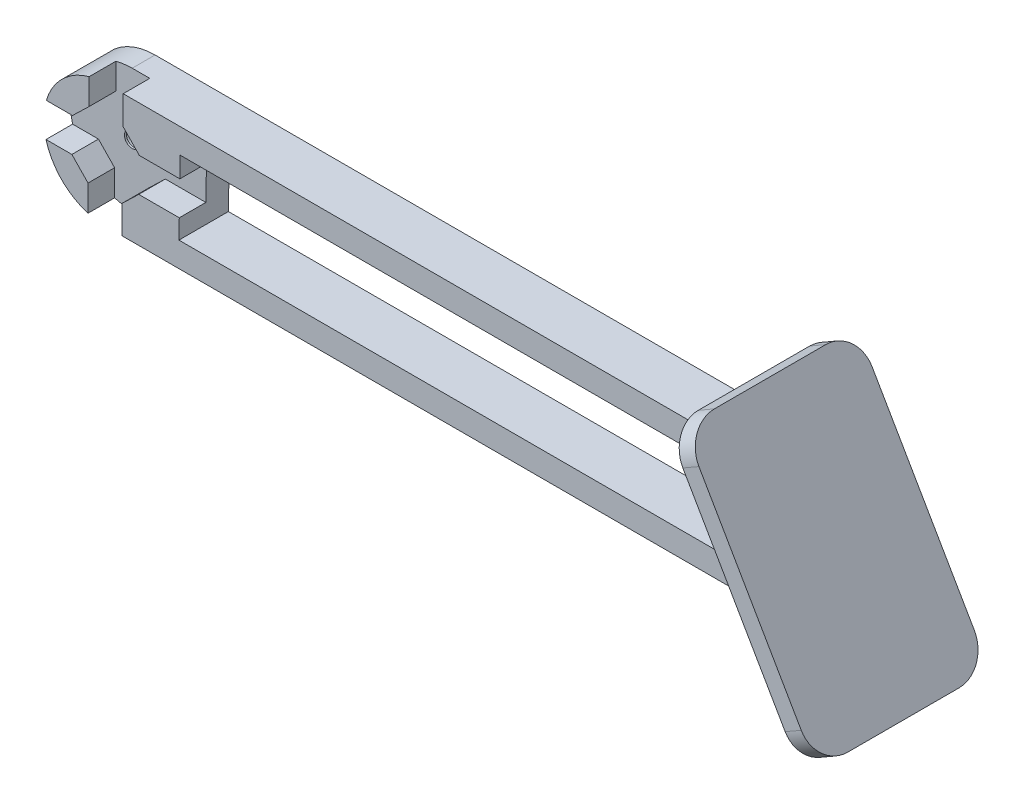
SolidWorks part; units mm, degrees
ref_plane "Plan de face" through (0, 0, 0) normal (0, 0, 1) x (1, 0, 0)
ref_plane "Plan de dessus" through (0, 0, 0) normal (0, 1, 0) x (1, 0, 0)
ref_plane "Plan de droite" through (0, 0, 0) normal (1, 0, 0) x (0, 0, -1)
sketch "Esquisse1" plane through (0, 0, 0) normal (0, 0, 1) x (1, 0, 0)
  line L0 (60, -10.9971) -> (60, 26.1419) construction
  line L1 (0, 0) -> (120, 0)
  line L3 (0, 20) -> (120, 20)
  arc A0 (0, 0) -> (0, 20) centre (0, 10) cw
  arc A1 (120, 0) -> (120, 20) centre (120, 10) ccw
  point P9 (60, 0)
  point P11 (60, 20)
  dimension "D3" = 10
  dimension "D1" = 20
  dimension "D2" = 60
extrude "Boss.-Extru.1" add sketch "Esquisse1" along normal blind 8
sketch "Esquisse13" plane through (0, 0, 8) normal (0, 0, 1) x (1, 0, 0)
  circle A0 centre (0, 10) radius 4
  arc A1 (0, 20) -> (0, 0) centre (0, 10) ccw construction
  dimension "D1" = 8
extrude "Enlèv. mat.-Extru.9" cut sketch "Esquisse13" against normal blind 4.3
sketch "Esquisse14" plane through (0, 0, 8) normal (0, 0, 1) x (1, 0, 0)
  line L0 (2.6554, 4.5441) -> (2.6554, -2.0086)
  line L1 (-2.6554, 22.0086) -> (2.8446, 21.9124)
  line L2 (-2.8446, -1.9124) -> (-2.8446, 4.6403)
  line L4 (12.0086, 12.6554) -> (11.9124, 7.1554)
  line L7 (2.6554, -2.0086) -> (-2.8446, -1.9124)
  line L10 (-12.0086, 7.3446) -> (-11.9124, 12.8446)
  line L12 (5.4559, 12.6554) -> (2.8446, 15.3597)
  line L13 (2.6554, 4.5441) -> (5.3597, 7.1554)
  line L14 (-2.6554, 15.4559) -> (-5.3597, 12.8446)
  line L15 (-5.4559, 7.3446) -> (-2.8446, 4.6403)
  line L16 (5.3597, 7.1554) -> (11.9124, 7.1554)
  line L17 (5.4559, 12.6554) -> (12.0086, 12.6554)
  line L18 (2.8446, 15.3597) -> (2.8446, 21.9124)
  line L19 (-2.6554, 15.4559) -> (-2.6554, 22.0086)
  line L20 (-5.3597, 12.8446) -> (-11.9124, 12.8446)
  line L21 (-5.4559, 7.3446) -> (-12.0086, 7.3446)
  circle A3 centre (0, 10) radius 6.0678 construction
  dimension "D1" = 5.5
  dimension "D2" = 6.5527
extrude "Enlèv. mat.-Extru.10" cut sketch "Esquisse14" against normal blind 4.3
sketch "Esquisse15" plane through (0, 0, 0) normal (0, 0, -1) x (-1, 0, 0)
  circle A0 centre (0, 10) radius 2.5
  arc A1 (0, 0) -> (0, 20) centre (0, 10) ccw construction
  dimension "D1" = 5
extrude "Enlèv. mat.-Extru.11" cut sketch "Esquisse15" against normal blind 3.4
sketch "Esquisse16" plane through (0, 0, 3.4) normal (0, 0, -1) x (-1, 0, 0)
  circle A0 centre (0, 10) radius 1.25
  circle A1 centre (0, 10) radius 2.5 construction
  dimension "D1" = 2.5
extrude "Enlèv. mat.-Extru.12" cut sketch "Esquisse16" against normal up to next
sketch "Esquisse17" plane through (0, 0, 8) normal (0, 0, 1) x (1, 0, 0)
  line L0 (120, 20) -> (2.8446, 20) construction
  line L1 (120, 20) -> (130, 20)
  line L2 (120, 20) -> (120, 0)
  line L3 (120, 0) -> (130, 0)
  line L4 (130, 20) -> (130, 0)
  line L5 (2.6554, 0) -> (120, 0) construction
  arc A0 (120, 0) -> (120, 20) centre (120, 10) ccw construction
extrude "Enlèv. mat.-Extru.13" cut sketch "Esquisse17" against normal blind 10
sketch "Esquisse19" plane through (0, 0, 0) normal (0, 0, -1) x (-1, 0, 0)
  line L0 (-131.547, 0) -> (-120, 0)
  line L1 (-131.547, 0) -> (-120, 20)
  line L2 (-120, 0) -> (-108.453, 20)
  line L3 (-120, 20) -> (-108.453, 20)
  line L4 (0, 0) -> (-120, 0) construction
  line L5 (-120, 20) -> (0, 20) construction
  line L15 (-120, 0) -> (-120, 20) construction
  dimension "D1" = 120
extrude "Enlèv. mat.-Extru.15" cut sketch "Esquisse19" against normal blind 10
sketch "Esquisse20" plane through (90, 51.9615, 0) normal (0.866, 0.5, 0) x (0, 0, -1)
  line L0 (-8, -60) -> (-8, -36.906) construction
  line L1 (-18, -70) -> (10, -70)
  line L2 (-18, -70) -> (-18, -26.906)
  line L3 (-18, -26.906) -> (10, -26.906)
  line L4 (10, -70) -> (10, -26.906)
  line L5 (0, -60) -> (0, -36.906) construction
  line L6 (-8, -36.906) -> (0, -36.906) construction
  line L7 (-8, -60) -> (0, -60) construction
  dimension "D1" = 10
  dimension "D2" = 10
  dimension "D3" = 10
  dimension "D4" = 10
extrude "Boss.-Extru.2" add sketch "Esquisse20" against normal blind 3
sketch "Esquisse21" plane through (0, 0, 8) normal (0, 0, 1) x (1, 0, 0)
  line L1 (11.8572, 4) -> (109.6077, 4)
  line L2 (11.8572, 4) -> (12.0671, 16)
  line L3 (12.0671, 16) -> (102.6795, 16)
  line L4 (109.6077, 4) -> (102.6795, 16)
  line L5 (11.9124, 7.1554) -> (12.0086, 12.6554) construction
  line L6 (116.5359, 0) -> (104.9889, 20) construction
  line L7 (2.6554, 0) -> (116.5359, 0) construction
  line L8 (104.9889, 20) -> (2.8446, 20) construction
  dimension "D1" = 4
  dimension "D2" = 4
  dimension "D3" = 4
extrude "Enlèv. mat.-Extru.16" cut sketch "Esquisse21" against normal up to next
fillet "Congé1" radius 5 4 edges at (102.154, 27.9103, 18) (102.154, 27.9103, -10) (123.701, -9.4103, -10) (123.701, -9.4103, 18)
